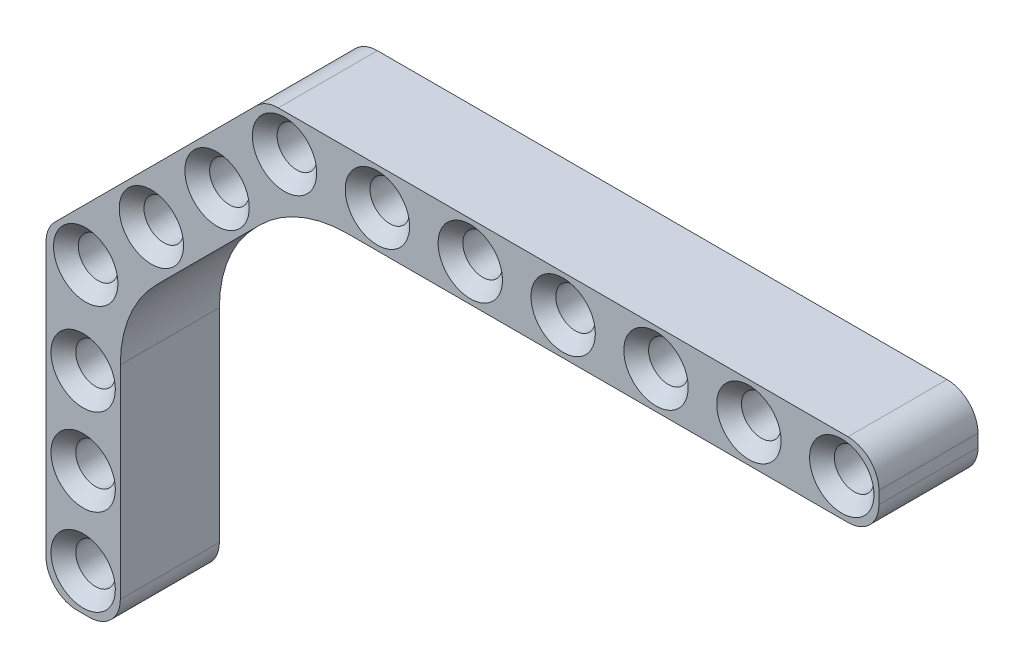
SolidWorks part; units mm, degrees
ref_plane "Front Plane" through (0, 0, 0) normal (0, 0, 1) x (1, 0, 0)
ref_plane "Top Plane" through (0, 0, 0) normal (0, 1, 0) x (1, 0, 0)
ref_plane "Right Plane" through (0, 0, 0) normal (1, 0, 0) x (0, 0, -1)
sketch "Sketch1" plane through (0, 0, 0) normal (0, 0, 1) x (1, 0, 0)
  line L1 (-0.5, 3) -> (45.5, 3)
  line L2 (-3, 0.5) -> (-3, -0.5)
  line L3 (-0.5, -3) -> (45.5, -3)
  line L4 (48, 0.5) -> (48, -0.5)
  circle A0 centre (0, 0) radius 1.6
  arc A1 (45.5, -3) -> (48, -0.5) centre (45.5, -0.5) ccw
  arc A2 (45.5, 3) -> (48, 0.5) centre (45.5, 0.5) cw
  arc A3 (-3, -0.5) -> (-0.5, -3) centre (-0.5, -0.5) ccw
  arc A4 (-0.5, 3) -> (-3, 0.5) centre (-0.5, 0.5) ccw
  circle A5 centre (7.5, 0) radius 1.6
  circle A6 centre (15, 0) radius 1.6
  circle A7 centre (22.5, 0) radius 1.6
  circle A8 centre (30, 0) radius 1.6
  circle A9 centre (37.5, 0) radius 1.6
  circle A10 centre (45, 0) radius 1.6
  point P8 (-3, 0)
  point P14 (-3, -3)
  point P17 (-3, 3)
  dimension "D1" = 3.2
  dimension "D4" = 2.5
  dimension "D2" = 6
  dimension "D3" = 3
  dimension "D6" = 7.5
  dimension "D5" = 7
extrude "Boss-Extrude1" add sketch "Sketch1" along normal blind 8
chamfer "Chamfer1" distance 1 angle 45 10 edges at (31.6, 0, 0) (31.6, 0, 8) (24.1, 0, 0) (24.1, 0, 8) (16.6, 0, 0) (16.6, 0, 8) (9.1, 0, 0) (9.1, 0, 8) (1.6, 0, 0) (1.6, 0, 8)
sketch "Sketch2" plane through (0, 0, 8) normal (0, 0, 1) x (1, 0, 0)
  line L0 (-2.2678, 2.2678) -> (-18.5292, -13.9937)
  line L1 (-18.5292, -17.5292) -> (-17.8221, -18.2363)
  line L2 (-14.2866, -18.2363) -> (0.9497, -3)
  line L4 (-0.5, -3) -> (45.5, -3) construction
  arc A0 (-0.5, 3) -> (-3, 0.5) centre (-0.5, 0.5) ccw construction
  circle A1 centre (-5.4477, -5.1548) radius 1.6
  circle A2 centre (-10.751, -10.4581) radius 1.6
  circle A3 centre (-16.0543, -15.7614) radius 1.6
  arc A4 (-18.5292, -13.9937) -> (-18.5292, -17.5292) centre (-16.7614, -15.7614) ccw
  arc A5 (-17.8221, -18.2363) -> (-14.2866, -18.2363) centre (-16.0543, -16.4685) ccw
  point P18 (-20.297, -15.7614)
  point P21 (-16.0543, -20.0041)
  arc M15 (-0.5, 3) -> (-3, 0.5) centre (-0.5, 0.5) ccw
  line M16 (-3, 0.5) -> (-3, -0.5)
  arc M17 (-3, -0.5) -> (-0.5, -3) centre (-0.5, -0.5) ccw
  line M18 (-0.5, -3) -> (45.5, -3)
  dimension "D3" = 3.2
  dimension "D8" = 2.5
  dimension "D1" = 6
  dimension "D2" = 45
  dimension "D4" = 3
  dimension "D5" = 7.5
  dimension "D7" = 3
  dimension "D6" = 3
extrude "Boss-Extrude3" add sketch "Sketch2" against normal blind 8 contours L1 A5 L2 L0 A4 A1 A2 A3 M18 M17 M16 M15
fillet "Fillet1" radius 10 1 edges at (0.9497, -3, 4)
chamfer "Chamfer2" distance 1 angle 45 6 edges at (-14.4543, -15.7614, 8) (-14.4543, -15.7614, 0) (-9.151, -10.4581, 8) (-9.151, -10.4581, 0) (-3.8477, -5.1548, 8) (-3.8477, -5.1548, 0)
chamfer "Chamfer3" distance 1 angle 45 4 edges at (46.6, 0, 0) (46.6, 0, 8) (39.1, 0, 0) (39.1, 0, 8)
sketch "Sketch3" plane through (0, 0, 8) normal (0, 0, 1) x (1, 0, 0)
  line L0 (-14.2866, -18.2363) -> (-1.9792, -5.9289) construction
  line L2 (-19.2614, -15.7614) -> (-19.2614, -37.7614)
  line L3 (-16.7614, -40.2614) -> (-15.7614, -40.2614)
  line L4 (-13.2614, -17.2112) -> (-13.2614, -37.7614)
  arc A0 (-18.5292, -13.9937) -> (-18.5292, -17.5292) centre (-16.7614, -15.7614) ccw construction
  circle A1 centre (-16.2614, -23.2614) radius 1.6
  circle A2 centre (-16.0543, -15.7614) radius 1.6 construction
  circle A3 centre (-16.2614, -30.2614) radius 1.6
  circle A4 centre (-16.2614, -37.2614) radius 1.6
  arc A5 (-19.2614, -37.7614) -> (-16.7614, -40.2614) centre (-16.7614, -37.7614) ccw
  arc A6 (-15.7614, -40.2614) -> (-13.2614, -37.7614) centre (-15.7614, -37.7614) ccw
  point P14 (-16.2614, -40.2614)
  point P20 (-19.2614, -40.2614)
  point P23 (-13.2614, -40.2614)
  arc M22 (-18.5292, -13.9937) -> (-18.5292, -17.5292) centre (-16.7614, -15.7614) ccw
  line M23 (-18.5292, -17.5292) -> (-17.8221, -18.2363)
  arc M24 (-17.8221, -18.2363) -> (-14.2866, -18.2363) centre (-16.0543, -16.4685) ccw
  line M25 (-14.2866, -18.2363) -> (-1.9792, -5.9289)
  dimension "D3" = 3.2
  dimension "D6" = 2.5
  dimension "D1" = 6
  dimension "D2" = 7.5
  dimension "D5" = 3
  dimension "D4" = 3
extrude "Boss-Extrude4" add sketch "Sketch3" against normal blind 8 contours L3 A6 L4 L2 A5 A1 A3 A4 M25 M24 M23 M22
chamfer "Chamfer5" distance 1 angle 45 6 edges at (-14.6614, -23.2614, 8) (-14.6614, -23.2614, 0) (-14.6614, -30.2614, 8) (-14.6614, -30.2614, 0) (-14.6614, -37.2614, 8) (-14.6614, -37.2614, 0)
fillet "Fillet2" radius 10 1 edges at (-13.2614, -17.2112, 4)
